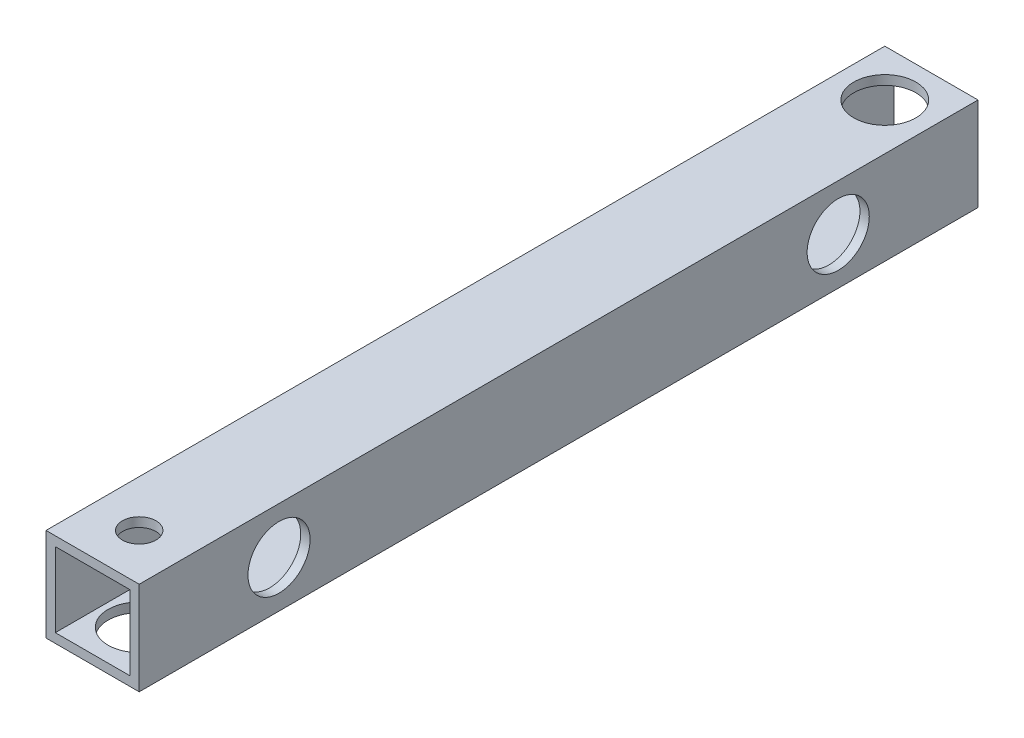
SolidWorks part; units mm, degrees
material "6063-T5"
ref_plane "正面" through (0, 0, 0) normal (0, 0, 1) x (1, 0, 0)
ref_plane "平面" through (0, 0, 0) normal (0, 1, 0) x (1, 0, 0)
ref_plane "右側面" through (0, 0, 0) normal (1, 0, 0) x (0, 0, -1)
sketch "ｽｹｯﾁ1" plane through (0, 0, 0) normal (0, 0, 1) x (1, 0, 0)
  line L1 (-7.5, -7.5) -> (7.5, -7.5)
  line L2 (-7.5, -7.5) -> (-7.5, 7.5)
  line L3 (-7.5, 7.5) -> (7.5, 7.5)
  line L4 (7.5, -7.5) -> (7.5, 7.5)
  line L5 (-7.5, -7.5) -> (7.5, 7.5) construction
  line L6 (-7.5, 7.5) -> (7.5, -7.5) construction
  line L7 (-6, -6) -> (6, -6)
  line L8 (-6, -6) -> (-6, 6)
  line L9 (-6, 6) -> (6, 6)
  line L10 (6, -6) -> (6, 6)
  line L11 (-6, -6) -> (6, 6) construction
  line L12 (-6, 6) -> (6, -6) construction
  point P0 (0, 0)
  point P6 (0, 0)
  dimension "D1" = 1.5
  dimension "D2" = 15
  dimension "D3" = 15
extrude "ﾎﾞｽ - 押し出し1" add sketch "ｽｹｯﾁ1" along normal blind 135
sketch "ｽｹｯﾁ2" plane through (7.5, 0, 0) normal (1, 0, 0) x (0, 0, -1)
  line L0 (-135, -7.5) -> (0, -7.5) construction
  line L2 (-135, -7.5) -> (-135, 7.5) construction
  circle A4 centre (-112.5, 0) radius 2.7
  circle A8 centre (-22.5, 0) radius 2.7
  dimension "D1" = 5.4
  dimension "D2" = 22.5
  dimension "D3" = 7.5
  dimension "D4" = 90
  dimension "D9" = 2
extrude "ｶｯﾄ - 押し出し1" cut sketch "ｽｹｯﾁ2" against normal blind 25
sketch "ｽｹｯﾁ3" plane through (0, 7.5, 0) normal (0, 1, 0) x (1, 0, 0)
  line L2 (7.5, -135) -> (7.5, 0) construction
  circle A1 centre (0, -7.5) radius 2.25
  circle A6 centre (0, -127.5) radius 2.7
  dimension "D2" = 120
  dimension "D3" = 4.5
  dimension "D9" = 7.5
  dimension "D11" = 7.5
  dimension "D4" = 7.5
  dimension "D5" = 5.4
extrude "ｶｯﾄ - 押し出し2" cut sketch "ｽｹｯﾁ3" against normal blind 25
sketch "ｽｹｯﾁ4" plane through (0, 7.5, 0) normal (0, 1, 0) x (1, 0, 0)
  circle A0 centre (0, -7.5) radius 5
  dimension "D2" = 10
extrude "ｶｯﾄ - 押し出し3" cut sketch "ｽｹｯﾁ4" against normal blind 10
sketch "ｽｹｯﾁ5" plane through (7.5, 0, 0) normal (1, 0, 0) x (0, 0, -1)
  circle A0 centre (-22.5, 0) radius 5
  circle A1 centre (-112.5, 0) radius 5
  dimension "D1" = 10
  dimension "D2" = 10
extrude "ｶｯﾄ - 押し出し4" cut sketch "ｽｹｯﾁ5" against normal blind 10
sketch "ｽｹｯﾁ6" plane through (0, -7.5, 0) normal (0, -1, 0) x (-1, 0, 0)
  circle A0 centre (0, -127.5) radius 5
  dimension "D1" = 10
extrude "ｶｯﾄ - 押し出し5" cut sketch "ｽｹｯﾁ6" against normal blind 10
